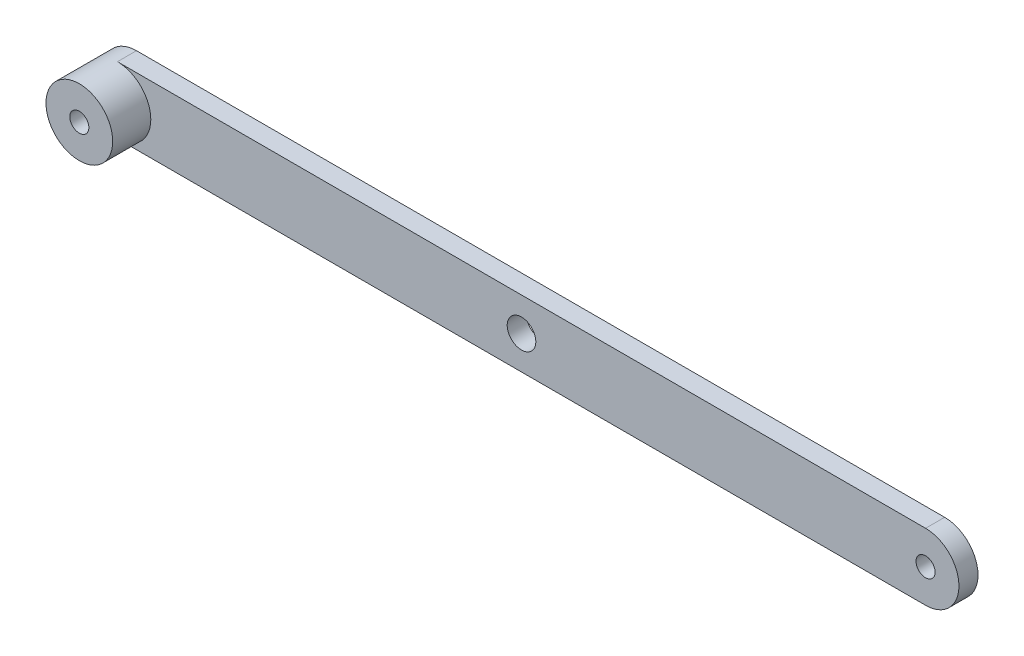
SolidWorks part; units mm, degrees
ref_plane "Alzado" through (0, 0, 0) normal (0, 0, 1) x (1, 0, 0)
ref_plane "Planta" through (0, 0, 0) normal (0, 1, 0) x (1, 0, 0)
ref_plane "Vista lateral" through (0, 0, 0) normal (1, 0, 0) x (0, 0, -1)
sketch "Croquis1" plane through (0, 0, 0) normal (0, 0, 1) x (1, 0, 0)
  line L0 (-212, 0) -> (212, 0) construction
  line L1 (-212, 17.5) -> (212, 17.5)
  line L2 (-212, -17.5) -> (212, -17.5)
  arc A0 (-212, 17.5) -> (-212, -17.5) centre (-212, 0) ccw
  arc A1 (212, -17.5) -> (212, 17.5) centre (212, 0) ccw
  circle A2 centre (-212, 0) radius 5
  circle A3 centre (212, 0) radius 5
  circle A4 centre (0, 0) radius 7.5
  point P2 (0, 0)
  dimension "D2" = 17.5
  dimension "D3" = 10
  dimension "D4" = 10
  dimension "D5" = 15
  dimension "D1" = 424
extrude "Saliente-Extruir1" add sketch "Croquis1" along normal blind 10
sketch "Croquis2" plane through (0, 0, 10) normal (0, 0, 1) x (1, 0, 0)
  circle A0 centre (-212, 0) radius 17.5
  circle A1 centre (-212, 0) radius 5
extrude "Saliente-Extruir2" add sketch "Croquis2" along normal blind 20
